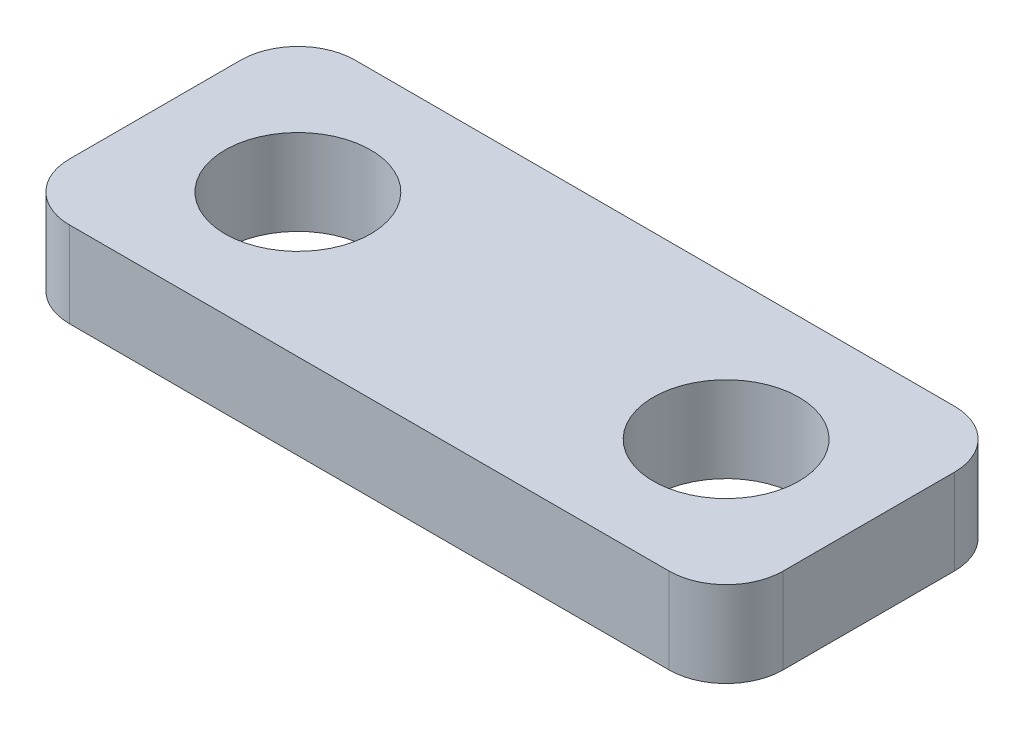
SolidWorks part; units mm, degrees
ref_plane "Front Plane" through (0, 0, 0) normal (0, 0, 1) x (1, 0, 0)
ref_plane "Top Plane" through (0, 0, 0) normal (0, 1, 0) x (1, 0, 0)
ref_plane "Right Plane" through (0, 0, 0) normal (1, 0, 0) x (0, 0, -1)
sketch "Sketch1" plane through (0, 0, 0) normal (0, 1, 0) x (1, 0, 0)
  line L0 (-12.5, 0) -> (12.5, 0) construction
  line L1 (-12.5, -5) -> (12.5, -5)
  line L2 (-12.5, -5) -> (-12.5, 5)
  line L3 (-12.5, 5) -> (12.5, 5)
  line L4 (12.5, -5) -> (12.5, 5)
  line L5 (-12.5, -5) -> (12.5, 5) construction
  line L6 (-12.5, 5) -> (12.5, -5) construction
  line L7 (0, 5) -> (0, -5) construction
  circle A0 centre (-7.5, 0) radius 2.55
  circle A1 centre (7.5, 0) radius 2.55
  point P0 (0, 0)
  point P14 (0, 0)
  dimension "D1" = 5.1
  dimension "D2" = 15
  dimension "D3" = 10
  dimension "D4" = 25
extrude "Boss-Extrude1" add sketch "Sketch1" along normal blind 3
fillet "Fillet1" radius 2 4 edges at (-12.5, 1.5, -5) (12.5, 1.5, -5) (12.5, 1.5, 5) (-12.5, 1.5, 5)
